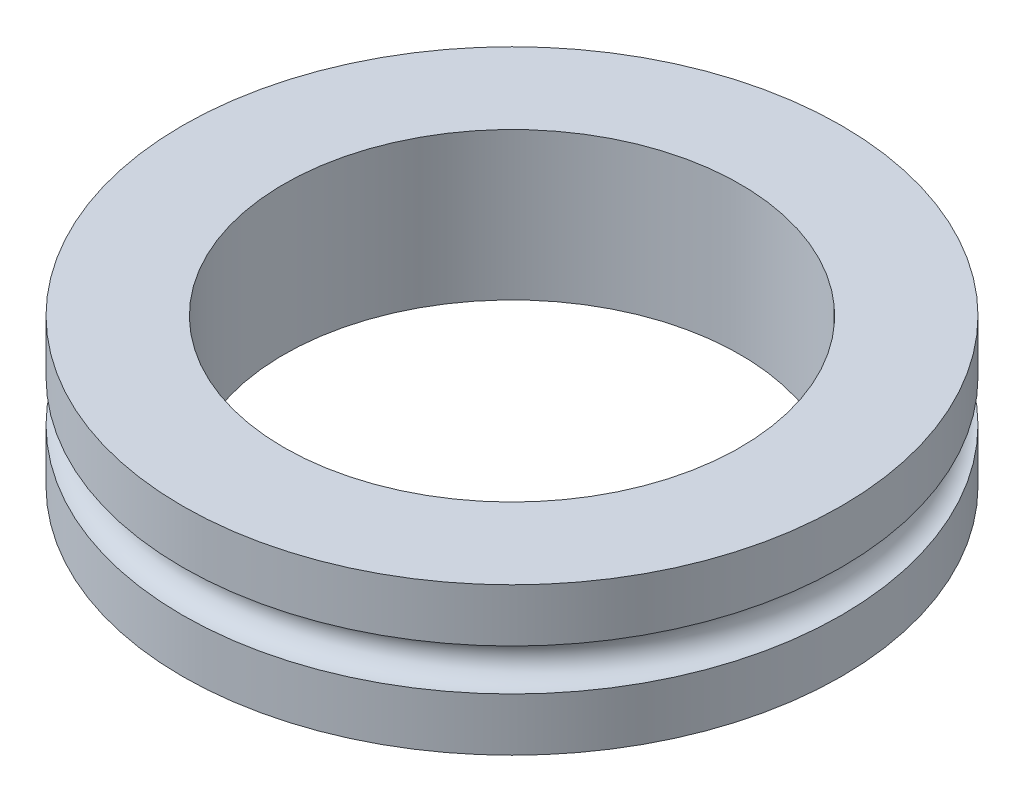
SolidWorks part; units mm, degrees
ref_plane "Front Plane" through (0, 0, 0) normal (0, 0, 1) x (1, 0, 0)
ref_plane "Top Plane" through (0, 0, 0) normal (0, 1, 0) x (1, 0, 0)
ref_plane "Right Plane" through (0, 0, 0) normal (1, 0, 0) x (0, 0, -1)
sketch "Sketch1" plane through (0, 0, 0) normal (0, 1, 0) x (1, 0, 0)
  circle A0 centre (0, 0) radius 15.875
  dimension "D1" = 31.75
extrude "Boss-Extrude1" add sketch "Sketch1" along normal blind 7.112
sketch "Sketch2" plane through (0, 0, 0) normal (0, 0, 1) x (1, 0, 0)
  line L0 (-15.875, 7.112) -> (-15.875, 0) construction
  line L2 (-15.875, 4.556) -> (-15.875, 2.556)
  line L3 (0, 7.112) -> (0, 0) construction
  line L4 (15.875, 7.112) -> (-15.875, 7.112) construction
  line L5 (-15.875, 0) -> (15.875, 0) construction
  arc A1 (-15.875, 4.556) -> (-15.875, 2.556) centre (-15.875, 3.556) cw
  point P3 (0, 0)
  point P6 (0, 3.556)
  dimension "D1" = 2
revolve "Cut-Revolve1" cut sketch "Sketch2" angle 360 about L3
sketch "Sketch4" plane through (0, 7.112, 0) normal (0, 1, 0) x (1, 0, 0)
  circle A0 centre (0, 0) radius 12.7
  circle A1 centre (0, 0) radius 7.62
  dimension "D1" = 25.4
  dimension "D2" = 15.24
sketch "Sketch3" plane through (0, 7.112, 0) normal (0, 1, 0) x (1, 0, 0)
  circle A1 centre (0, 0) radius 10.9919
  dimension "D1" = 21.9837
extrude "Cut-Extrude1" cut sketch "Sketch3" against normal blind 10.16
